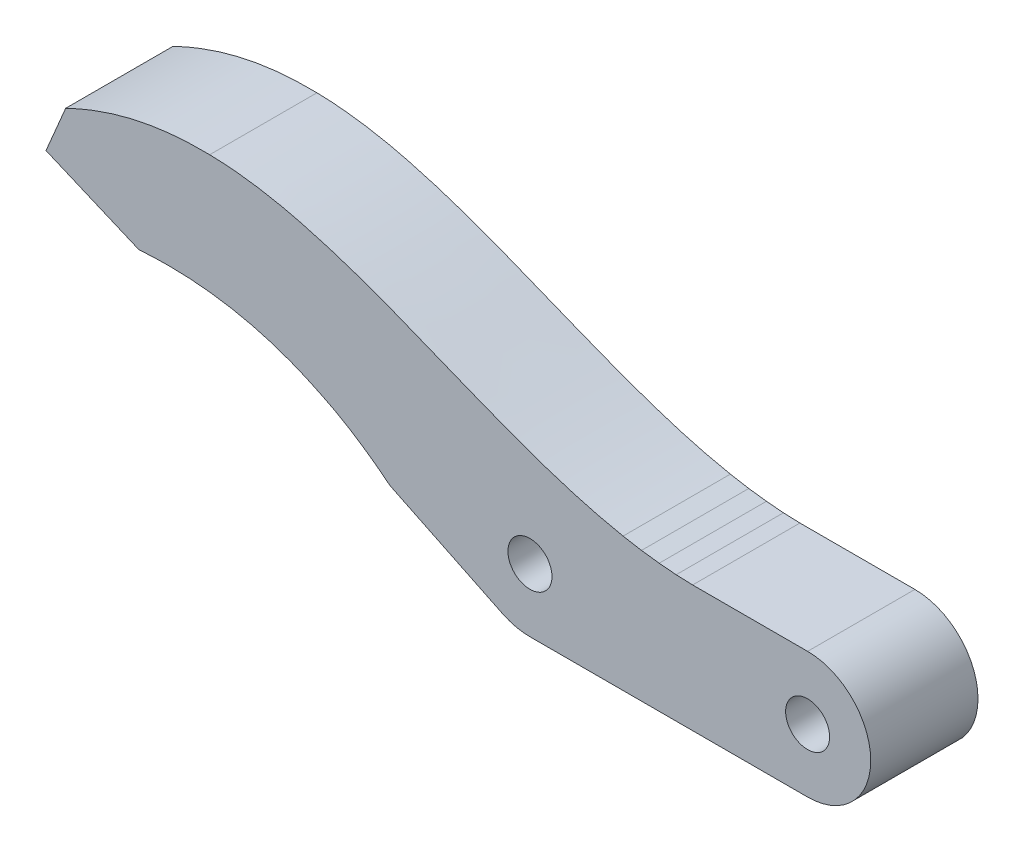
SolidWorks part; units mm, degrees
ref_plane "Alzado" through (0, 0, 0) normal (0, 0, 1) x (1, 0, 0)
ref_plane "Planta" through (0, 0, 0) normal (0, 1, 0) x (1, 0, 0)
ref_plane "Vista lateral" through (0, 0, 0) normal (1, 0, 0) x (0, 0, -1)
sketch "Croquis1" plane through (0, 0, 0) normal (0, 0, 1) x (1, 0, 0)
  line L0 (-8.694, 5) -> (0, 5)
  line L1 (-22, -5) -> (0, -5)
  line L2 (-33.0828, -0.176) -> (-24.1811, -4.497)
  line L3 (-33.0828, -0.176) -> (-34.1508, 0.655)
  line L4 (-36.3298, 2.134) -> (-35.2358, 1.426)
  line L5 (-37.4338, 2.78) -> (-36.3298, 2.134)
  line L6 (-38.5928, 3.367) -> (-37.4338, 2.78)
  line L7 (-35.2358, 1.426) -> (-34.1508, 0.655)
  line L8 (-60.3458, 9.189) -> (-52.9808, 6.067)
  line L9 (-60.3458, 9.189) -> (-58.7858, 12.872)
  line L10 (-9.11, 5) -> (-8.694, 5)
  line L11 (-10.416, 5.05) -> (-9.11, 5)
  line L12 (-11.763, 5.166) -> (-10.416, 5.05)
  line L13 (-13.161, 5.346) -> (-11.763, 5.166)
  line L14 (-14.621, 5.599) -> (-13.161, 5.346)
  circle A0 centre (0, 0) radius 1.743
  arc A1 (0, 5) -> (0, -5) centre (0, 0) cw
  circle A2 centre (-22, 0) radius 1.745
  spline S0 degree 3 poles (-22, -5) (-22.3761, -5.0007) (-23.1279, -4.912) (-23.8427, -4.6627) (-24.1811, -4.497) knots 0 0 0 0 0.499596 1 1 1 1
  spline S1 degree 3 poles (-38.5928, 3.367) (-39.3325, 3.7346) (-40.4636, 4.2337) (-42.0098, 4.7896) (-43.1803, 5.1503) (-44.3674, 5.4555) (-45.5716, 5.707) (-46.795, 5.9028) (-48.465, 6.0938) (-49.7333, 6.151) (-50.5848, 6.154) knots 0 0 0 0 0.199499 0.29823 0.396705 0.495216 0.594152 0.693711 0.794352 1 1 1 1
  spline S2 degree 2 poles (-50.5848, 6.154) (-51.7845, 6.1561) (-52.9808, 6.067) knots 0 0 0 1 1 1
  spline S3 degree 3 poles (-14.621, 5.599) (-15.5632, 5.7811) (-17.011, 6.1208) (-18.9894, 6.6847) (-20.6355, 7.2081) (-22.4399, 7.8347) (-24.5401, 8.6199) (-27.0914, 9.6314) (-29.9008, 10.7725) (-32.585, 11.8399) (-34.7946, 12.6654) (-36.6022, 13.2928) (-38.193, 13.7965) (-39.6719, 14.2117) (-41.0683, 14.5763) (-42.4025, 14.8517) (-43.6944, 15.0783) (-45.342, 15.2923) (-46.5685, 15.3718) (-47.3769, 15.389) knots 0 0 0 0 0.083834 0.129856 0.179713 0.234727 0.296727 0.3756 0.474504 0.561663 0.627975 0.680575 0.728822 0.773739 0.814774 0.854889 0.892721 0.929358 1 1 1 1
  spline S4 degree 3 poles (-47.3769, 15.389) (-48.1969, 15.4033) (-49.3983, 15.3797) (-50.9708, 15.2246) (-52.0988, 15.0613) (-53.22, 14.8413) (-54.3361, 14.567) (-55.4494, 14.235) (-56.9506, 13.7078) (-58.056, 13.227) (-58.7858, 12.872) knots 0 0 0 0 0.208581 0.305129 0.401666 0.498318 0.595561 0.693826 0.793635 1 1 1 1
  point P10 (-22.5621, -4.968)
  point P11 (-23.1181, -4.872)
  point P12 (-23.6601, -4.715)
  point P13 (-24.1811, -4.497)
  point P14 (-33.0828, -0.176)
  point P18 (-34.1508, 0.655)
  point P20 (-35.2358, 1.426)
  point P22 (-36.3298, 2.134)
  point P23 (-37.4338, 2.78)
  point P24 (-38.5928, 3.367)
  point P25 (-39.7198, 3.895)
  point P26 (-40.8598, 4.366)
  point P27 (-42.0138, 4.781)
  point P28 (-43.1828, 5.141)
  point P29 (-44.3678, 5.446)
  point P30 (-45.5708, 5.697)
  point P31 (-46.7918, 5.893)
  point P32 (-48.0338, 6.035)
  point P33 (-49.2978, 6.122)
  point P34 (-50.5848, 6.154)
  point P35 (-51.8968, 6.129)
  point P36 (-52.9808, 6.067)
  point P45 (-60.3458, 9.189)
  point P51 (-58.7858, 12.872)
  point P53 (-9.11, 5)
  point P57 (-14.621, 5.599)
  point P59 (-13.161, 5.346)
  point P61 (-11.763, 5.166)
  point P62 (-10.416, 5.05)
  point P63 (-15.99, 5.89)
  point P64 (-17.425, 6.248)
  point P65 (-18.945, 6.68)
  point P66 (-20.577, 7.197)
  point P67 (-22.362, 7.815)
  point P68 (-24.357, 8.558)
  point P69 (-30.027, 10.819)
  point P70 (-32.811, 11.917)
  point P71 (-38.232, 13.799)
  point P72 (-34.945, 12.711)
  point P73 (-36.652, 13.301)
  point P74 (-39.716, 14.219)
  point P75 (-42.4293, 14.85)
  point P76 (-41.0813, 14.567)
  point P77 (-43.7094, 15.071)
  point P78 (-44.9569, 15.233)
  point P79 (-26.877, 9.55)
  point P80 (-46.1809, 15.338)
  point P81 (-47.3769, 15.389)
  point P82 (-57.6648, 13.387)
  point P83 (-56.5518, 13.838)
  point P84 (-55.4408, 14.228)
  point P85 (-54.3298, 14.559)
  point P86 (-53.2158, 14.833)
  point P87 (-52.0968, 15.052)
  point P88 (-50.9698, 15.216)
  point P89 (-48.6836, 15.384)
  point P90 (-49.8362, 15.327)
  dimension "D1" = 3.486
  dimension "D6" = 3.49
  dimension "D2" = 5
  dimension "D3" = 5
  dimension "D4" = 8.694
  dimension "D5" = 22
  dimension "D7" = 5
  dimension "D8" = 0.563
  dimension "D9" = 0.556
  dimension "D10" = 0.542
  dimension "D11" = 0.521
  dimension "D12" = 4.968
  dimension "D13" = 4.872
  dimension "D14" = 4.715
  dimension "D15" = 4.497
  dimension "D16" = 4.824
  dimension "D17" = 9.895
  dimension "D18" = 1.068
  dimension "D19" = 5.655
  dimension "D20" = 6.426
  dimension "D21" = 1.085
  dimension "D22" = 1.094
  dimension "D23" = 7.134
  dimension "D24" = 1.104
  dimension "D25" = 7.78
  dimension "D26" = 1.159
  dimension "D27" = 8.367
  dimension "D28" = 1.127
  dimension "D29" = 8.895
  dimension "D30" = 1.14
  dimension "D31" = 9.366
  dimension "D32" = 1.154
  dimension "D33" = 9.781
  dimension "D34" = 1.169
  dimension "D35" = 10.141
  dimension "D36" = 1.185
  dimension "D37" = 10.446
  dimension "D38" = 1.203
  dimension "D39" = 10.697
  dimension "D40" = 1.221
  dimension "D41" = 10.893
  dimension "D42" = 1.242
  dimension "D43" = 11.035
  dimension "D44" = 1.264
  dimension "D45" = 11.122
  dimension "D46" = 1.287
  dimension "D47" = 11.154
  dimension "D48" = 1.312
  dimension "D49" = 11.129
  dimension "D50" = 1.084
  dimension "D51" = 11.067
  dimension "D52" = 7.365
  dimension "D53" = 14.189
  dimension "D54" = 1.56
  dimension "D55" = 17.872
  dimension "D56" = 5
  dimension "D57" = 0.416
  dimension "D58" = 1.306
  dimension "D59" = 5.05
  dimension "D60" = 1.347
  dimension "D61" = 5.166
  dimension "D62" = 1.398
  dimension "D63" = 5.346
  dimension "D64" = 1.46
  dimension "D65" = 5.599
  dimension "D66" = 1.369
  dimension "D67" = 5.89
  dimension "D68" = 1.435
  dimension "D69" = 6.248
  dimension "D70" = 1.52
  dimension "D71" = 6.68
  dimension "D72" = 1.632
  dimension "D73" = 7.197
  dimension "D74" = 1.785
  dimension "D75" = 7.815
  dimension "D76" = 1.995
  dimension "D77" = 8.558
  dimension "D78" = 2.52
  dimension "D79" = 9.55
  dimension "D80" = 3.15
  dimension "D81" = 10.819
  dimension "D82" = 2.784
  dimension "D83" = 11.917
  dimension "D84" = 2.134
  dimension "D85" = 12.711
  dimension "D86" = 1.707
  dimension "D87" = 13.301
  dimension "D88" = 1.58
  dimension "D89" = 1.484
  dimension "D90" = 13.799
  dimension "D91" = 14.219
  dimension "D92" = 1.409
  dimension "D93" = 1.348
  dimension "D94" = 1.299
  dimension "D95" = 1.258
  dimension "D96" = 1.224
  dimension "D97" = 1.196
  dimension "D98" = 14.567
  dimension "D99" = 14.85
  dimension "D100" = 15.071
  dimension "D101" = 15.233
  dimension "D102" = 15.338
  dimension "D103" = 15.389
  dimension "D104" = 1.121
  dimension "D105" = 7.32
  dimension "D106" = 1.113
  dimension "D107" = 7.771
  dimension "D108" = 1.111
  dimension "D109" = 8.161
  dimension "D110" = 1.111
  dimension "D111" = 1.114
  dimension "D112" = 1.119
  dimension "D113" = 1.127
  dimension "D114" = 1.139
  dimension "D115" = 1.154
  dimension "D116" = 8.492
  dimension "D117" = 8.766
  dimension "D118" = 8.985
  dimension "D119" = 9.149
  dimension "D120" = 9.26
  dimension "D121" = 9.317
extrude "Saliente-Extruir1" add sketch "Croquis1" along normal blind 8.5
